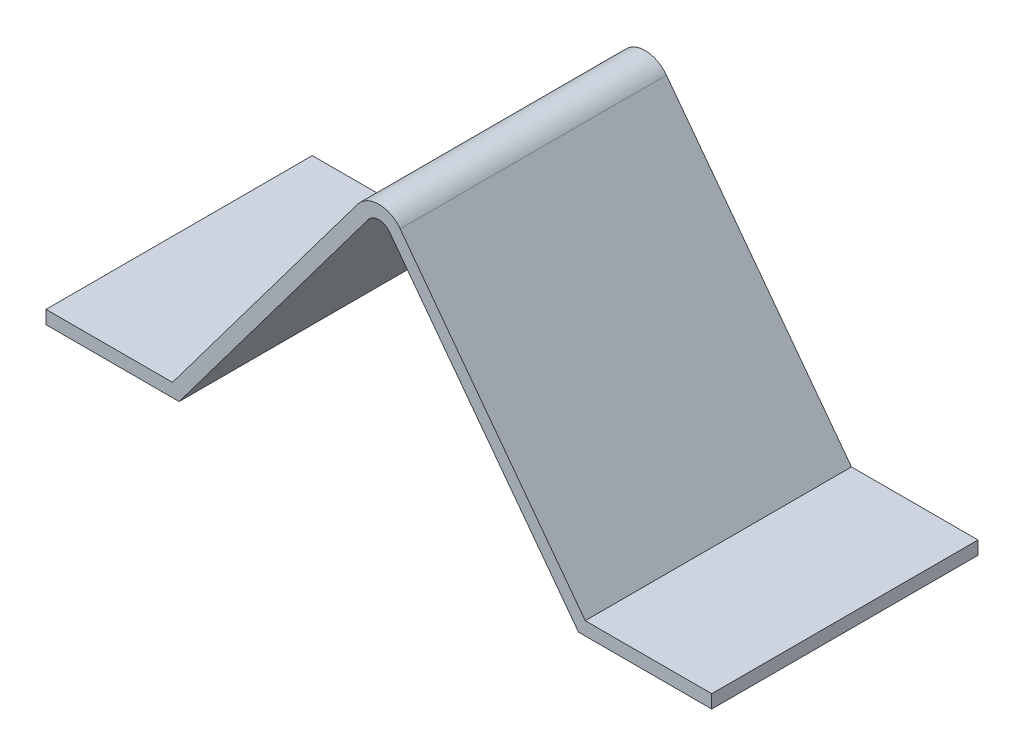
SolidWorks part; units mm, degrees
ref_plane "前视基准面" through (0, 0, 0) normal (0, 0, 1) x (1, 0, 0)
ref_plane "上视基准面" through (0, 0, 0) normal (0, 1, 0) x (1, 0, 0)
ref_plane "右视基准面" through (0, 0, 0) normal (1, 0, 0) x (0, 0, -1)
sketch "草图1" plane through (0, 0, 0) normal (0, 0, 1) x (1, 0, 0)
  line L0 (0, 0) -> (0, 12.953) construction
  line L1 (-15, 0) -> (0, 20)
  line L2 (-15, 0) -> (-25, 0)
  line L3 (15, 0) -> (25, 0)
  line L4 (15, 0) -> (0, 20)
  line L5 (15.5, 1) -> (25, 1)
  line L6 (15.5, 1) -> (0, 21.6667)
  line L7 (-15.5, 1) -> (0, 21.6667)
  line L8 (-15.5, 1) -> (-25, 1)
  line L9 (25, 0) -> (25, 1)
  line L10 (-25, 0) -> (-25, 1)
  dimension "D1" = 30
  dimension "D2" = 20
  dimension "D3" = 10
  dimension "D4" = 1
extrude "凸台-拉伸1" add sketch "草图1" along normal mid plane 20
fillet "圆角1" radius 1 1 edges at (0, 20, 0)
fillet "圆角2" radius 2 1 edges at (0, 21.6667, 0)
